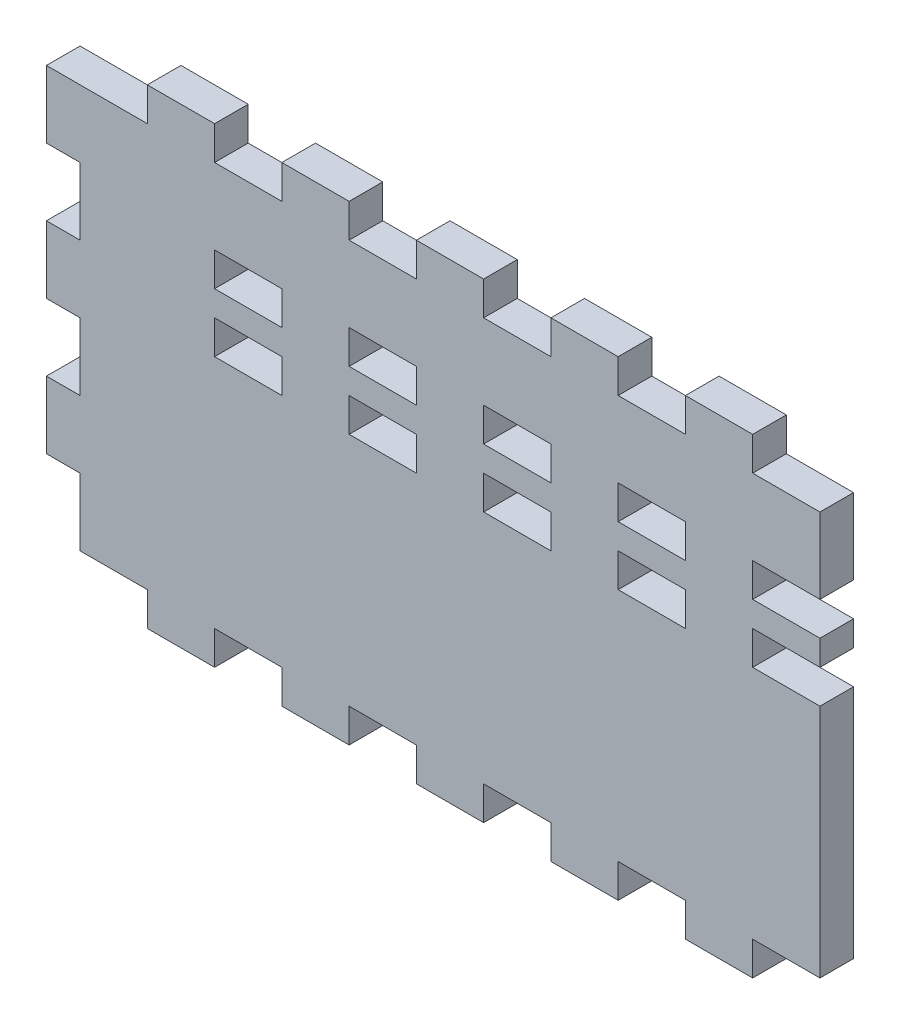
SolidWorks part; units mm, degrees
ref_plane "Front Plane" through (0, 0, 0) normal (0, 0, 1) x (1, 0, 0)
ref_plane "Top Plane" through (0, 0, 0) normal (0, 1, 0) x (1, 0, 0)
ref_plane "Right Plane" through (0, 0, 0) normal (1, 0, 0) x (0, 0, -1)
sketch "Sketch1" plane through (0, 0, 0) normal (0, 0, 1) x (1, 0, 0)
  line L1 (-139.7, -76.2) -> (139.7, -76.2)
  line L2 (-139.7, -76.2) -> (-139.7, 76.2)
  line L3 (-139.7, 76.2) -> (139.7, 76.2)
  line L4 (139.7, -76.2) -> (139.7, 76.2)
  line L5 (-139.7, -76.2) -> (139.7, 76.2) construction
  line L6 (-139.7, 76.2) -> (139.7, -76.2) construction
  point P0 (0, 0)
  dimension "D1" = 279.4
  dimension "D2" = 152.4
extrude "Boss-Extrude1" add sketch "Sketch1" along normal blind 12.7
sketch "Sketch2" plane through (0, -76.2, 0) normal (0, -1, 0) x (1, 0, 0)
  line L0 (-139.7, 0) -> (139.7, 0) construction
  line L1 (-114.3, 0) -> (-88.9, 0)
  line L2 (-114.3, 0) -> (-114.3, 12.7)
  line L3 (-114.3, 12.7) -> (-88.9, 12.7)
  line L4 (-88.9, 0) -> (-88.9, 12.7)
  line L5 (-139.7, 12.7) -> (139.7, 12.7) construction
  line L6 (-139.7, 12.7) -> (-139.7, 0) construction
  point P10 (-139.7, 6.35)
  dimension "D1" = 25.4
  dimension "D2" = 25.4
extrude "Boss-Extrude2" add sketch "Sketch2" along normal blind 12.7
pattern_linear "LPattern1" count 5 spacing 50.8 along (1, 0, 0) of "Boss-Extrude2"
mirror "Mirror1" about plane through (0, 0, 0) normal (0, 1, 0) of "LPattern1", "Boss-Extrude2"
sketch "Sketch3" plane through (-139.7, 0, 0) normal (-1, 0, 0) x (0, 0, 1)
  line L0 (0, 76.2) -> (0, -76.2) construction
  line L1 (12.7, 76.2) -> (0, 76.2)
  line L2 (12.7, 76.2) -> (12.7, 50.8)
  line L3 (12.7, 50.8) -> (0, 50.8)
  line L4 (0, 76.2) -> (0, 50.8)
  dimension "D1" = 25.4
extrude "Boss-Extrude3" add sketch "Sketch3" along normal blind 12.7
pattern_linear "LPattern2" count 3 spacing 50.8 along (0, -1, 0) of "Boss-Extrude3"
sketch "Sketch4" plane through (0, 0, 0) normal (0, 0, -1) x (-1, 0, 0)
  line L1 (-139.7, 12.7) -> (-114.3, 12.7)
  line L2 (-139.7, 12.7) -> (-139.7, 25.4)
  line L3 (-139.7, 25.4) -> (-114.3, 25.4)
  line L4 (-114.3, 12.7) -> (-114.3, 25.4)
  line L5 (-114.3, -76.2) -> (-139.7, -76.2) construction
  line L6 (-139.7, -76.2) -> (-139.7, 76.2) construction
  dimension "D1" = 25.4
  dimension "D2" = 12.7
  dimension "D4" = 88.9
extrude "Cut-Extrude1" cut sketch "Sketch4" against normal through all
pattern_linear "LPattern3" count 5 spacing 50.8 along (-1, 0, 0) of "Cut-Extrude1"
sketch "Sketch5" plane through (0, 0, 12.7) normal (0, 0, 1) x (1, 0, 0)
  line L0 (-88.9, 12.7) -> (-88.9, 25.4) construction
  line L1 (-63.5, 47.625) -> (-88.9, 47.625)
  line L2 (-63.5, 47.625) -> (-63.5, 34.925)
  line L3 (-63.5, 34.925) -> (-88.9, 34.925)
  line L4 (-88.9, 47.625) -> (-88.9, 34.925)
  line L6 (-88.9, -76.2) -> (-63.5, -76.2) construction
  point P8 (-76.2, -76.2)
  dimension "D1" = 25.4
  dimension "D2" = 12.7
  dimension "D3" = 123.825
extrude "Cut-Extrude2" cut sketch "Sketch5" against normal through all
pattern_linear "LPattern4" count 5 spacing 50.8 along (1, 0, 0) of "Cut-Extrude2"
